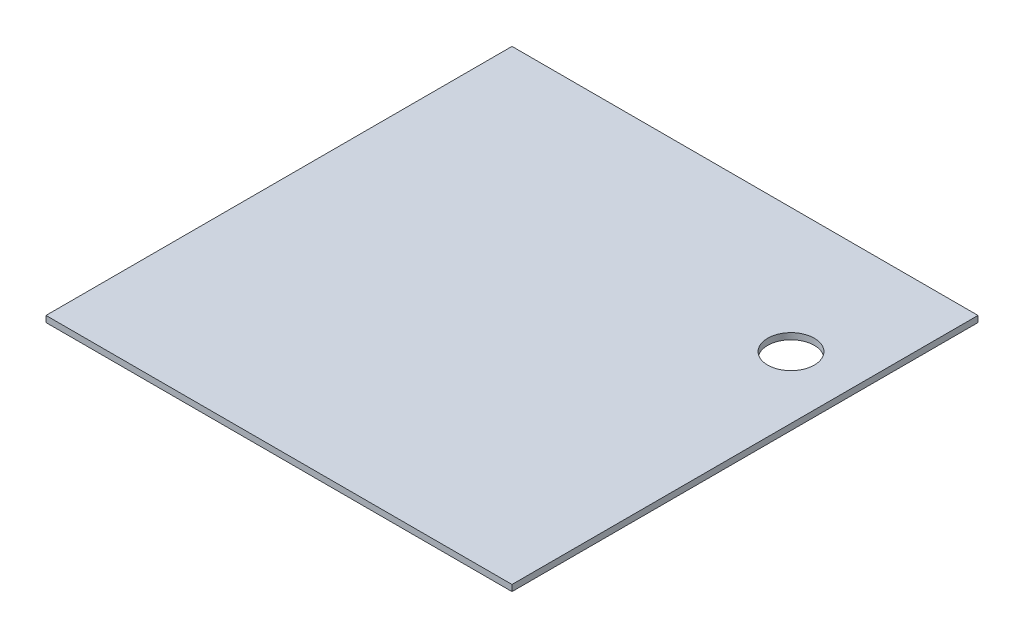
SolidWorks part; units mm, degrees
ref_plane "Front Plane" through (0, 0, 0) normal (0, 0, 1) x (1, 0, 0)
ref_plane "Top Plane" through (0, 0, 0) normal (0, 1, 0) x (1, 0, 0)
ref_plane "Right Plane" through (0, 0, 0) normal (1, 0, 0) x (0, 0, -1)
sketch "Sketch1" plane through (0, 0, 0) normal (0, 1, 0) x (1, 0, 0)
  line L1 (-75, 75) -> (75, 75)
  line L2 (-75, 75) -> (-75, -75)
  line L3 (-75, -75) -> (75, -75)
  line L4 (75, 75) -> (75, -75)
  line L5 (-75, 75) -> (75, -75) construction
  line L6 (-75, -75) -> (75, 75) construction
  point P0 (0, 0)
  dimension "D1" = 150
  dimension "D2" = 150
extrude "Boss-Extrude1" add sketch "Sketch1" along normal blind 2
sketch "Sketch2" plane through (0, 2, 0) normal (0, 1, 0) x (1, 0, 0)
  line L0 (75, -75) -> (75, 75) construction
  line L1 (-75, -75) -> (75, -75) construction
  point P0 (55, -50)
  dimension "D1" = 20
  dimension "D2" = 25
sketch "Sketch3" plane through (0, 2, 0) normal (0, 1, 0) x (1, 0, 0)
  line L0 (-75, -75) -> (75, -75) construction
  line L1 (-75, 75) -> (-75, -75) construction
  line L2 (75, 75) -> (-75, 75) construction
  line L3 (75, -75) -> (75, 75) construction
  point P0 (-55, -50)
  point P1 (-55, 50)
  point P2 (55, 50)
  dimension "D1" = 25
  dimension "D2" = 20
  dimension "D3" = 20
  dimension "D4" = 25
  dimension "D5" = 20
  dimension "D6" = 25
sketch "Sketch4" plane through (0, 2, 0) normal (0, 1, 0) x (1, 0, 0)
  line L0 (-75, 75) -> (-75, -75) construction
  line L1 (-75, 7.1446) -> (-45, 7.1446)
  line L2 (-75, 7.1446) -> (-75, -17.8554)
  line L3 (-75, -17.8554) -> (-45, -17.8554)
  line L4 (-45, 7.1446) -> (-45, -17.8554)
  point P6 (-60, -17.8554)
  dimension "D1" = 30
  dimension "D2" = 25
sketch "Sketch5" plane through (0, 2, 0) normal (0, 1, 0) x (1, 0, 0)
  circle A0 centre (55, 34.807) radius 7.5
  dimension "D1" = 15
extrude "Cut-Extrude1" cut sketch "Sketch5" against normal up to next
